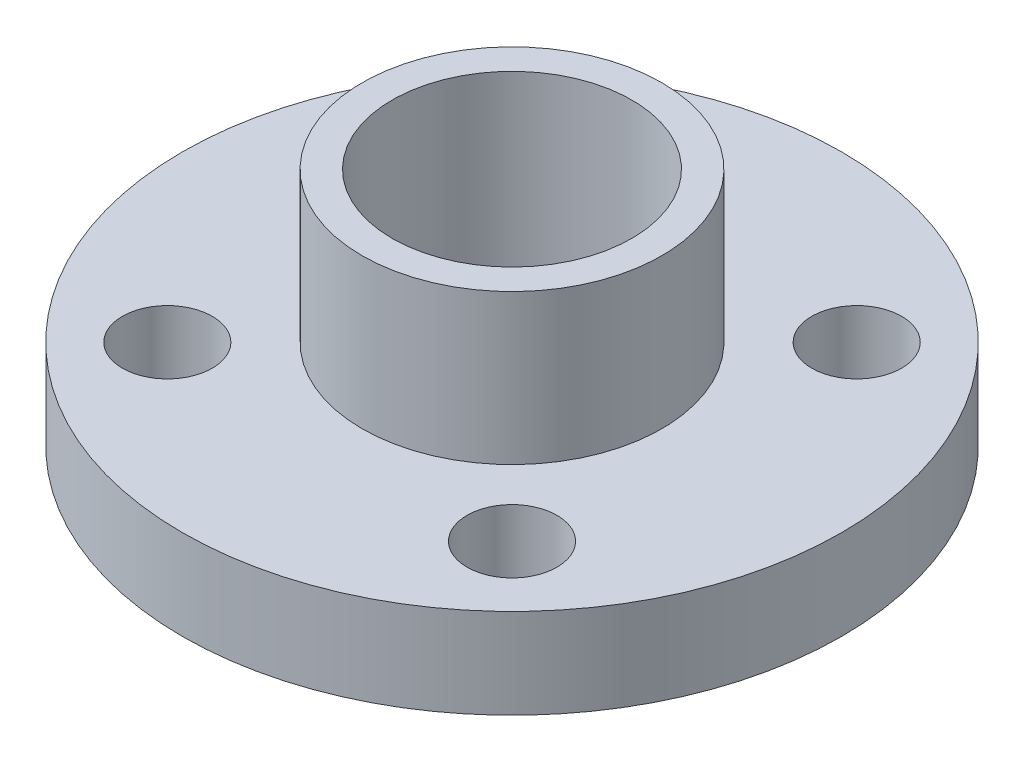
SolidWorks part; units mm, degrees
ref_plane "Front Plane" through (0, 0, 0) normal (0, 0, 1) x (1, 0, 0)
ref_plane "Top Plane" through (0, 0, 0) normal (0, 1, 0) x (1, 0, 0)
ref_plane "Right Plane" through (0, 0, 0) normal (1, 0, 0) x (0, 0, -1)
sketch "Sketch1" plane through (0, 0, 0) normal (0, 1, 0) x (1, 0, 0)
  circle A0 centre (0, 0) radius 11
  circle A1 centre (0, 0) radius 5
  circle A2 centre (-5.75, 5.75) radius 1.5
  circle A3 centre (5.75, 5.75) radius 1.5
  circle A4 centre (5.75, -5.75) radius 1.5
  circle A5 centre (-5.75, -5.75) radius 1.5
  point P15 (0, 0)
  dimension "D1" = 10
  dimension "D2" = 22
  dimension "D3" = 3
  dimension "D4" = 5.75
  dimension "D5" = 5.75
  dimension "D6" = 4
extrude "Boss-Extrude1" add sketch "Sketch1" along normal blind 3
sketch "Sketch2" plane through (0, 0, 0) normal (0, 1, 0) x (1, 0, 0)
  circle A0 centre (0, 0) radius 5
  circle A1 centre (0, 0) radius 4
  dimension "D1" = 10
  dimension "D2" = 8
extrude "Boss-Extrude2" add sketch "Sketch2" along normal blind 8 and the other way blind 2
